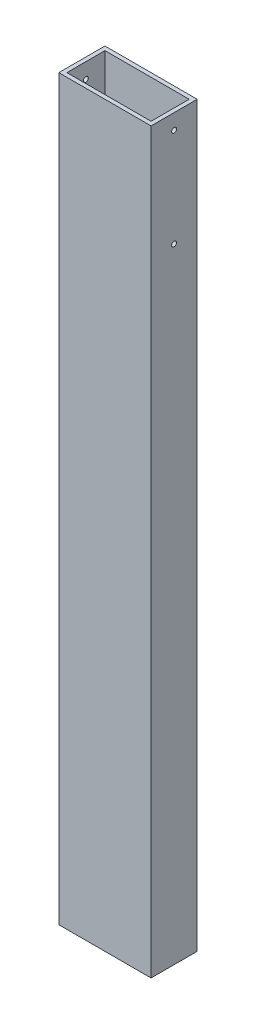
SolidWorks part; units mm, degrees
ref_plane "Front Plane" through (0, 0, 0) normal (0, 0, 1) x (1, 0, 0)
ref_plane "Top Plane" through (0, 0, 0) normal (0, 1, 0) x (1, 0, 0)
ref_plane "Right Plane" through (0, 0, 0) normal (1, 0, 0) x (0, 0, -1)
sketch "Sketch1" plane through (0, 0, 0) normal (0, 1, 0) x (1, 0, 0)
  line L1 (-19.05, -9.525) -> (19.05, -9.525)
  line L2 (-19.05, -9.525) -> (-19.05, 9.525)
  line L3 (-19.05, 9.525) -> (19.05, 9.525)
  line L4 (19.05, -9.525) -> (19.05, 9.525)
  line L7 (-17.399, -7.874) -> (17.399, -7.874)
  line L8 (-17.399, -7.874) -> (-17.399, 7.874)
  line L9 (-17.399, 7.874) -> (17.399, 7.874)
  line L10 (17.399, -7.874) -> (17.399, 7.874)
  point P0 (0, 7.874)
  point P6 (0, 9.525)
  point P11 (-19.05, 0)
  point P13 (-17.399, 0)
  dimension "D1" = 38.1
  dimension "D2" = 19.05
  dimension "D3" = 1.651
  dimension "D4" = 1.651
extrude "Boss-Extrude1" add sketch "Sketch1" along normal blind 304.8
sketch "Sketch2" plane through (19.05, 0, 0) normal (1, 0, 0) x (0, 0, -1)
  line L0 (-9.525, 304.8) -> (9.525, 304.8) construction
  line L1 (-7.874, 304.8) -> (7.874, 304.8) construction
  circle A0 centre (0, 298.45) radius 1.016
  circle A1 centre (0, 257.81) radius 1.016
  point P6 (0, 304.8)
  point P7 (0, 304.8)
  dimension "D1" = 2.032
  dimension "D2" = 40.64
  dimension "D3" = 6.35
extrude "Cut-Extrude1" cut sketch "Sketch2" against normal through all
